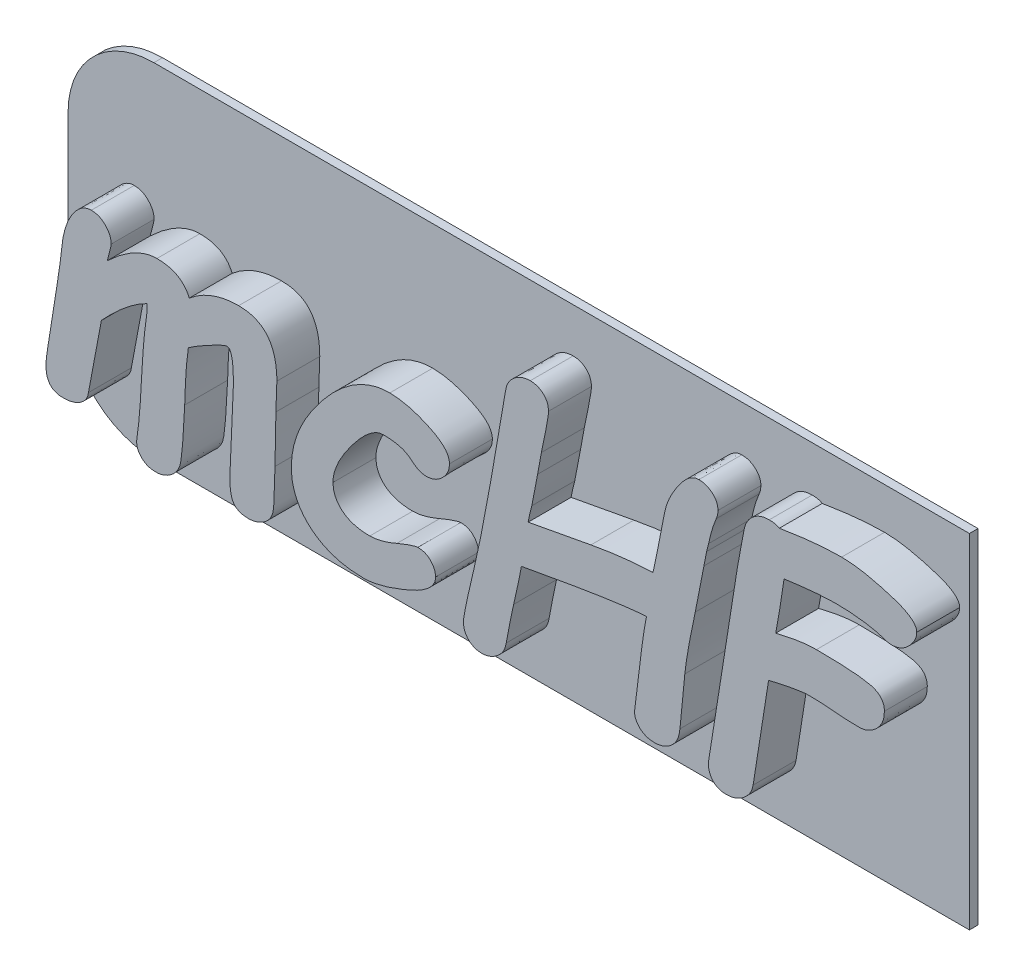
SolidWorks part; units mm, degrees
ref_plane "Front Plane" through (0, 0, 0) normal (0, 0, 1) x (1, 0, 0)
ref_plane "Top Plane" through (0, 0, 0) normal (0, 1, 0) x (1, 0, 0)
ref_plane "Right Plane" through (0, 0, 0) normal (1, 0, 0) x (0, 0, -1)
sketch "Sketch1" plane through (0, 0, 0) normal (0, 0, 1) x (1, 0, 0)
  line L1 (10.5, -4) -> (-10.5, -4)
  line L2 (10.5, -4) -> (10.5, 4)
  line L3 (10.5, 4) -> (-10.5, 4)
  line L4 (-10.5, -4) -> (-10.5, 4)
  line L5 (10.5, -4) -> (-10.5, 4) construction
  line L6 (10.5, 4) -> (-10.5, -4) construction
  point P0 (0, 0)
  dimension "D1" = 21
  dimension "D2" = 8
extrude "body" add sketch "Sketch1" along normal blind 0.2
sketch "Sketch2" plane through (0, 0, 0.2) normal (0, 0, 1) x (1, 0, 0)
  line L0 (-10.5, -4) -> (10.5, -4) construction
  line L1 (-10.5, 4) -> (-10.5, -4) construction
  text T0 "mcHF" font "Comic Sans MS" height in points 20
  dimension "D1" = 1.25
  dimension "D2" = 0.1
extrude "text" add sketch "Sketch2" along normal blind 1
fillet "Fillet1" radius 2 2 edges at (-10.5, 4, 0.1) (-10.5, -4, 0.1)
